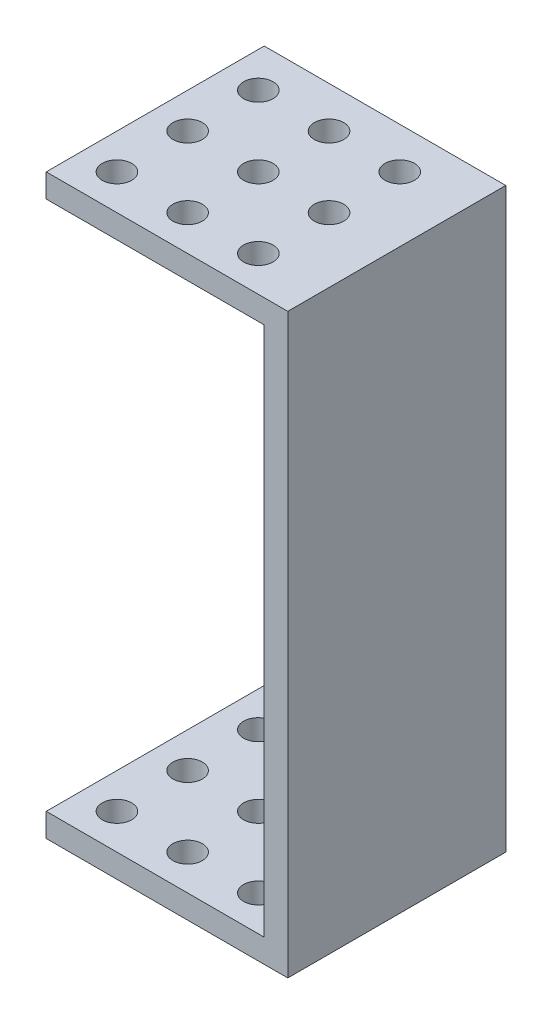
SolidWorks part; units mm, degrees
ref_plane "Front Plane" through (0, 0, 0) normal (0, 0, 1) x (1, 0, 0)
ref_plane "Top Plane" through (0, 0, 0) normal (0, 1, 0) x (1, 0, 0)
ref_plane "Right Plane" through (0, 0, 0) normal (1, 0, 0) x (0, 0, -1)
sketch "Sketch1" plane through (0, 0, 0) normal (0, 1, 0) x (1, 0, 0)
  line L1 (10.25, -9.25) -> (-10.25, -9.25)
  line L2 (10.25, -9.25) -> (10.25, 9.25)
  line L3 (10.25, 9.25) -> (-10.25, 9.25)
  line L4 (-10.25, -9.25) -> (-10.25, 9.25)
  line L5 (10.25, -9.25) -> (-10.25, 9.25) construction
  line L6 (10.25, 9.25) -> (-10.25, -9.25) construction
  point P0 (0, 0)
  dimension "D1" = 20.5
  dimension "D2" = 18.5
extrude "Boss-Extrude1" add sketch "Sketch1" along normal blind 2
sketch "Sketch2" plane through (0, 2, 0) normal (0, 1, 0) x (1, 0, 0)
  line L0 (-10.25, 9.25) -> (10.25, -9.25) construction
  line L1 (10.25, 9.25) -> (-10.25, -9.25) construction
  line L3 (10.25, 9.25) -> (-10.25, 9.25) construction
  line L5 (10.25, -9.25) -> (8.25, -9.25)
  line L7 (8.25, -9.25) -> (8.25, 9.25)
  line L8 (8.25, 9.25) -> (10.25, 9.25)
  line L9 (-10.25, -9.25) -> (10.25, -9.25) construction
  line L12 (10.25, 9.25) -> (10.25, -9.25)
  dimension "D2" = 2
extrude "Boss-Extrude2" add sketch "Sketch2" along normal blind 45
sketch "Sketch3" plane through (0, 0, 0) normal (0, -1, 0) x (1, 0, 0)
  line L0 (-7.25, 6.25) -> (-7.25, 9.25) construction
  line L1 (-7.25, 6.25) -> (-10.25, 6.25) construction
  line L2 (-10.25, -9.25) -> (-10.25, 9.25) construction
  line L7 (-10.25, 9.25) -> (10.25, 9.25) construction
  circle A0 centre (-7.25, 6.25) radius 1.25
  dimension "D1" = 2.5
  dimension "D2" = 3
  dimension "D3" = 3
sketch "Sketch4" plane through (0, 47, 0) normal (0, 1, 0) x (1, 0, 0)
  line L1 (-10.25, 9.25) -> (10.25, 9.25)
  line L2 (-10.25, 9.25) -> (-10.25, -9.25)
  line L3 (-10.25, -9.25) -> (10.25, -9.25)
  line L4 (10.25, 9.25) -> (10.25, -9.25)
  line L5 (-10.25, 9.25) -> (10.25, -9.25) construction
  line L6 (-10.25, -9.25) -> (10.25, 9.25) construction
  point P0 (0, 0)
  dimension "D1" = 20.5
  dimension "D2" = 18.5
extrude "Boss-Extrude3" add sketch "Sketch4" along normal blind 2
extrude "Cut-Extrude1" cut sketch "Sketch3" against normal through all
pattern_linear "LPattern1" count 3 spacing 6 along (0, 0, -1) count 3 spacing 6 along (1, 0, 0) of "Cut-Extrude1"
